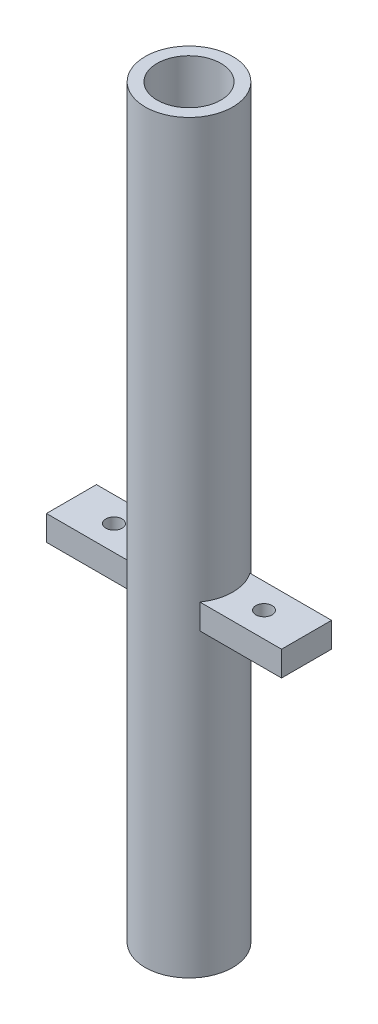
SolidWorks part; units mm, degrees
material "Plain Carbon Steel"
ref_plane "Front Plane" through (0, 0, 0) normal (0, 0, 1) x (1, 0, 0)
ref_plane "Top Plane" through (0, 0, 0) normal (0, 1, 0) x (1, 0, 0)
ref_plane "Right Plane" through (0, 0, 0) normal (1, 0, 0) x (0, 0, -1)
sketch "Sketch1" plane through (0, 0, 0) normal (0, 1, 0) x (1, 0, 0)
  circle A0 centre (0, 0) radius 12.75
  circle A1 centre (0, 0) radius 17.5
  dimension "D1" = 25.5
  dimension "D2" = 35
extrude "Boss-Extrude1" add sketch "Sketch1" along normal mid plane 298
ref_plane "Plane sets base of Plate surface - Don't move :)" through (0, -29, 0) normal (0, -1, 0) x (-1, 0, 0)
sketch "Sketch3" plane through (0, -29, 0) normal (0, -1, 0) x (-1, 0, 0)
  line L0 (0, 0) -> (0, 72.7303) construction
  line L1 (47, -10) -> (7.9096, -10)
  line L2 (47, -10) -> (47, 10)
  line L3 (47, 10) -> (7.9096, 10)
  line L4 (-47, -10) -> (-47, 10)
  line L5 (47, -10) -> (-47, 10) construction
  line L6 (47, 10) -> (-47, -10) construction
  line L7 (-7.9096, 10) -> (-47, 10)
  line L8 (-7.9096, -10) -> (-47, -10)
  circle A0 centre (0, 0) radius 12.75 construction
  arc A1 (-7.9096, 10) -> (-7.9096, -10) centre (0, 0) ccw
  circle A2 centre (-30, 0) radius 3.25
  circle A3 centre (30, 0) radius 3.25
  arc A4 (7.9096, 10) -> (7.9096, -10) centre (0, 0) cw
  point P0 (0, 0)
  point P14 (0, 0)
  dimension "D4" = 6.5
  dimension "D1" = 20
  dimension "D2" = 94
  dimension "D3" = 60
extrude "Boss-Extrude2" add sketch "Sketch3" against normal blind 10
